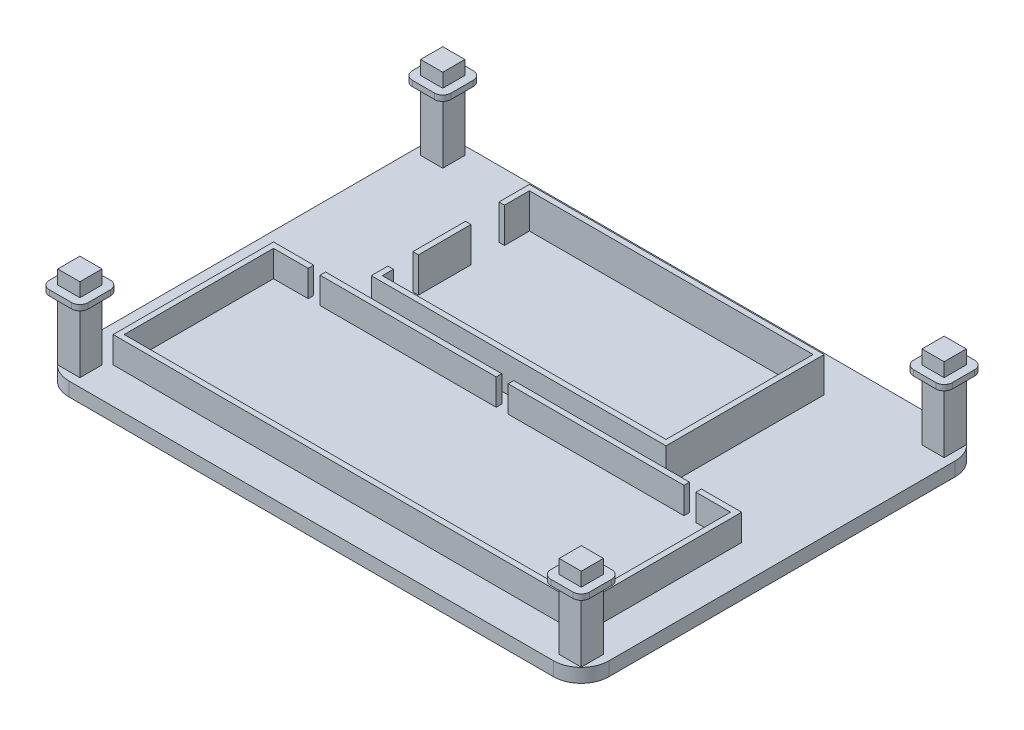
SolidWorks part; units mm, degrees
ref_plane "Front Plane" through (0, 0, 0) normal (0, 0, 1) x (1, 0, 0)
ref_plane "Top Plane" through (0, 0, 0) normal (0, 1, 0) x (1, 0, 0)
ref_plane "Right Plane" through (0, 0, 0) normal (1, 0, 0) x (0, 0, -1)
sketch "Sketch1" plane through (0, 0, 0) normal (0, 1, 0) x (1, 0, 0)
  line L0 (-97.5, 72.5) -> (97.5, -72.5) construction
  line L1 (-97.5, 72.5) -> (97.5, 72.5)
  line L2 (-97.5, 72.5) -> (-97.5, -72.5)
  line L3 (-97.5, -72.5) -> (97.5, -72.5)
  line L4 (97.5, 72.5) -> (97.5, -72.5)
  line L5 (97.5, 72.5) -> (-97.5, -72.5) construction
  point P4 (0, 0)
  dimension "D1" = 195
  dimension "D2" = 145
extrude "Boss-Extrude1" add sketch "Sketch1" along normal blind 5 contours L3 L4 L1 L2
sketch "Sketch2" plane through (0, 5, 0) normal (0, 1, 0) x (1, 0, 0)
  line L0 (-97.5, 72.5) -> (-97.5, -72.5) construction
  line L1 (-82.5, -3.6) -> (82.5, -3.6)
  line L2 (-82.5, -3.6) -> (-82.5, -57.5)
  line L3 (-82.5, -57.5) -> (82.5, -57.5)
  line L4 (82.5, -3.6) -> (82.5, -57.5)
  line L5 (97.5, 72.5) -> (97.5, -72.5) construction
  line L6 (97.5, 72.5) -> (97.5, -72.5)
  line L7 (-97.5, -72.5) -> (97.5, -72.5) construction
  line L8 (-84.5, -1.6) -> (84.5, -1.6)
  line L9 (84.5, -1.6) -> (84.5, -59.5)
  line L10 (-84.5, -59.5) -> (84.5, -59.5)
  line L11 (-84.5, -1.6) -> (-84.5, -59.5)
  line L12 (-70, -1.6) -> (-70, -3.6)
  line L13 (70, -1.6) -> (70, -3.6)
  line L14 (-2.1, -1.6) -> (-2.1, -3.6)
  line L15 (-65.7, -1.6) -> (-65.7, -3.6)
  line L16 (2.2, -1.6) -> (2.2, -3.6)
  line L17 (65.7, -1.6) -> (65.7, -3.6)
  point P20 (-2.1, -2.6)
  dimension "D1" = 165
  dimension "D2" = 15
  dimension "D3" = 53.9
  dimension "D4" = 15
  dimension "D6" = 12.5
  dimension "D7" = 12.5
  dimension "D8" = 80.4
  dimension "D9" = 4.3
  dimension "D10" = 4.3
  dimension "D11" = 4.3
  dimension "D5" = 2
extrude "Boss-Extrude2" add sketch "Sketch2" along normal blind 9.5 contours L8 L13 L1 L4 L3 L2 L12 L11 L10 L9 | L8 L15 L1 L14 | L17 L8 L16 L1
sketch "Sketch3" plane through (0, 5, 0) normal (0, 1, 0) x (1, 0, 0)
  line L0 (-97.5, 72.5) -> (97.5, 72.5) construction
  line L1 (-51.2, 57.5) -> (51.2, 57.5)
  line L2 (-51.2, 57.5) -> (-51.2, 4.4)
  line L3 (-51.2, 4.4) -> (51.2, 4.4)
  line L4 (51.2, 57.5) -> (51.2, 4.4)
  line L6 (97.5, 72.5) -> (97.5, -72.5) construction
  line L7 (-53.2, 59.5) -> (53.2, 59.5)
  line L8 (53.2, 59.5) -> (53.2, 2.4)
  line L9 (-53.2, 2.4) -> (53.2, 2.4)
  line L10 (-53.2, 59.5) -> (-53.2, 2.4)
  line L11 (-53.2, 48.5) -> (-51.2, 48.5)
  line L12 (-53.2, 17.4) -> (-51.2, 17.4)
  line L13 (-53.2, 36.4) -> (-51.2, 36.4)
  line L15 (-53.2, 8.4) -> (-51.2, 8.4)
  dimension "D1" = 53.1
  dimension "D2" = 102.4
  dimension "D3" = 15
  dimension "D4" = 46.3
  dimension "D6" = 9
  dimension "D7" = 12.1
  dimension "D8" = 4
  dimension "D9" = 9
  dimension "D5" = 2
sketch "Sketch4" plane through (0, 5, 0) normal (0, 1, 0) x (1, 0, 0)
  line L0 (-97.5, -72.5) -> (97.5, -72.5) construction
  line L1 (-94.5, -61.5) -> (-86.5, -61.5)
  line L2 (-94.5, -61.5) -> (-94.5, -69.5)
  line L3 (-94.5, -69.5) -> (-86.5, -69.5)
  line L4 (-86.5, -61.5) -> (-86.5, -69.5)
  line L5 (-97.5, 72.5) -> (-97.5, -72.5) construction
  line L6 (0, -7.975) -> (0, 7.975) construction
  line L7 (94.5, -61.5) -> (94.5, -69.5)
  line L8 (94.5, -69.5) -> (86.5, -69.5)
  line L9 (86.5, -61.5) -> (86.5, -69.5)
  line L10 (94.5, -61.5) -> (86.5, -61.5)
  line L11 (-7.975, 0) -> (7.975, 0) construction
  line L12 (94.5, 61.5) -> (86.5, 61.5)
  line L13 (94.5, 61.5) -> (94.5, 69.5)
  line L14 (94.5, 69.5) -> (86.5, 69.5)
  line L15 (86.5, 61.5) -> (86.5, 69.5)
  line L16 (-86.5, 61.5) -> (-86.5, 69.5)
  line L17 (-94.5, 69.5) -> (-86.5, 69.5)
  line L18 (-94.5, 61.5) -> (-94.5, 69.5)
  line L19 (-94.5, 61.5) -> (-86.5, 61.5)
  dimension "D1" = 8
  dimension "D2" = 3
  dimension "D3" = 3
extrude "Boss-Extrude3" add sketch "Sketch4" along normal blind 30
sketch "Sketch5" plane through (0, 35, 0) normal (0, 1, 0) x (1, 0, 0)
  line L0 (-97.5, 72.5) -> (97.5, 72.5) construction
  line L1 (97.5, 72.5) -> (97.5, -72.5) construction
  line L2 (-97.5, -72.5) -> (97.5, -72.5) construction
  line L3 (-97.5, 72.5) -> (-97.5, -72.5) construction
  line L4 (-97.5, 72.5) -> (97.5, 72.5)
  line L5 (97.5, 72.5) -> (97.5, -72.5)
  line L6 (-97.5, -72.5) -> (97.5, -72.5)
  line L7 (-97.5, 72.5) -> (-97.5, -72.5)
  line L9 (-97.5, 72.5) -> (97.5, 72.5)
  line L10 (-97.5, 72.5) -> (-97.5, -72.5)
  line L11 (-97.5, -72.5) -> (97.5, -72.5)
  line L12 (97.5, 72.5) -> (97.5, -72.5)
  point P0 (97.5, -72.5)
  point P4 (-97.5, 72.5)
extrude "Boss-Extrude11" add sketch "Sketch3" along normal blind 12.6 contours L13 L10 L12 L2 | L15 L10 L9 L8 L7 L11 L2 L1 L4 L3
ref_plane "Plane2" through (0, 30, 0) normal (0, 1, 0) x (1, 0, 0)
sketch "Sketch8" plane through (0, 30, 0) normal (0, 1, 0) x (1, 0, 0)
  line L0 (94.5, 61.5) -> (94.5, 69.5) construction
  line L1 (94.5, 69.5) -> (86.5, 69.5) construction
  line L2 (86.5, 69.5) -> (86.5, 61.5) construction
  line L3 (86.5, 61.5) -> (94.5, 61.5) construction
  line L4 (94.5, -61.5) -> (86.5, -61.5) construction
  line L5 (86.5, -61.5) -> (86.5, -69.5) construction
  line L6 (86.5, -69.5) -> (94.5, -69.5) construction
  line L7 (94.5, -69.5) -> (94.5, -61.5) construction
  line L8 (-94.5, -61.5) -> (-94.5, -69.5) construction
  line L9 (-94.5, -69.5) -> (-86.5, -69.5) construction
  line L10 (-86.5, -69.5) -> (-86.5, -61.5) construction
  line L11 (-86.5, -61.5) -> (-94.5, -61.5) construction
  line L12 (-94.5, 61.5) -> (-86.5, 61.5) construction
  line L13 (-86.5, 61.5) -> (-86.5, 69.5) construction
  line L14 (-86.5, 69.5) -> (-94.5, 69.5) construction
  line L15 (-94.5, 69.5) -> (-94.5, 61.5) construction
  line L16 (94.5, 61.5) -> (94.5, 69.5)
  line L17 (94.5, 69.5) -> (86.5, 69.5)
  line L18 (86.5, 69.5) -> (86.5, 61.5)
  line L19 (86.5, 61.5) -> (94.5, 61.5)
  line L20 (94.5, -61.5) -> (86.5, -61.5)
  line L21 (86.5, -61.5) -> (86.5, -69.5)
  line L22 (86.5, -69.5) -> (94.5, -69.5)
  line L23 (94.5, -69.5) -> (94.5, -61.5)
  line L24 (-94.5, -61.5) -> (-94.5, -69.5)
  line L25 (-94.5, -69.5) -> (-86.5, -69.5)
  line L26 (-86.5, -69.5) -> (-86.5, -61.5)
  line L27 (-86.5, -61.5) -> (-94.5, -61.5)
  line L28 (-94.5, 61.5) -> (-86.5, 61.5)
  line L29 (-86.5, 61.5) -> (-86.5, 69.5)
  line L30 (-86.5, 69.5) -> (-94.5, 69.5)
  line L31 (-94.5, 69.5) -> (-94.5, 61.5)
  line L32 (-94.5, 69.5) -> (-86.5, 61.5)
  line L33 (-86.5, 69.5) -> (-94.5, 61.5)
  line L34 (-97.5, 72.5) -> (97.5, 72.5) construction
  line L35 (-97.5, 58.5) -> (-83.5, 58.5)
  line L36 (-97.5, 58.5) -> (-97.5, 72.5)
  line L37 (-97.5, 72.5) -> (-83.5, 72.5)
  line L38 (-83.5, 58.5) -> (-83.5, 72.5)
  line L39 (-97.5, 58.5) -> (-83.5, 72.5) construction
  line L40 (-97.5, 72.5) -> (-83.5, 58.5) construction
  line L41 (-19.25, 0) -> (19.25, 0) construction
  line L42 (-97.5, -72.5) -> (-83.5, -72.5)
  line L43 (-97.5, -58.5) -> (-97.5, -72.5)
  line L44 (-83.5, -58.5) -> (-83.5, -72.5)
  line L45 (-97.5, -58.5) -> (-83.5, -58.5)
  line L46 (0, -19.25) -> (0, 19.25) construction
  line L47 (97.5, 72.5) -> (83.5, 72.5)
  line L48 (97.5, 58.5) -> (97.5, 72.5)
  line L49 (83.5, 58.5) -> (83.5, 72.5)
  line L50 (97.5, 58.5) -> (83.5, 58.5)
  line L51 (97.5, -58.5) -> (83.5, -58.5)
  line L52 (97.5, -58.5) -> (97.5, -72.5)
  line L53 (97.5, -72.5) -> (83.5, -72.5)
  line L54 (83.5, -58.5) -> (83.5, -72.5)
  point P14 (-90.5, 65.5)
extrude "Boss-Extrude12" add sketch "Sketch8" along direction (0, 1, 0) on the side against the normal blind 2 contours L50 L48 L47 L49 L19 L18 L17 L16 | L51 L54 L53 L52 L23 L22 L21 L20 | L45 L43 L42 L44 L27 L26 L25 L24 | L35 L38 L37 L36 L31 L30 L29 L28
fillet "Fillet2" radius 10 4 edges at (97.5, 2.5, 72.5) (-97.5, 2.5, 72.5) (-97.5, 2.5, -72.5) (97.5, 2.5, -72.5)
fillet "Fillet3" radius 3 16 edges at (-83.5, 29, -58.5) (-97.5, 29, -58.5) (-83.5, 29, -72.5) (-97.5, 29, -72.5) (-97.5, 29, 72.5) (-97.5, 29, 58.5) (-83.5, 29, 72.5) (-83.5, 29, 58.5) (97.5, 29, 72.5) (83.5, 29, 72.5) (97.5, 29, 58.5) (83.5, 29, 58.5) (83.5, 29, -58.5) (83.5, 29, -72.5) (97.5, 29, -58.5) (97.5, 29, -72.5)
